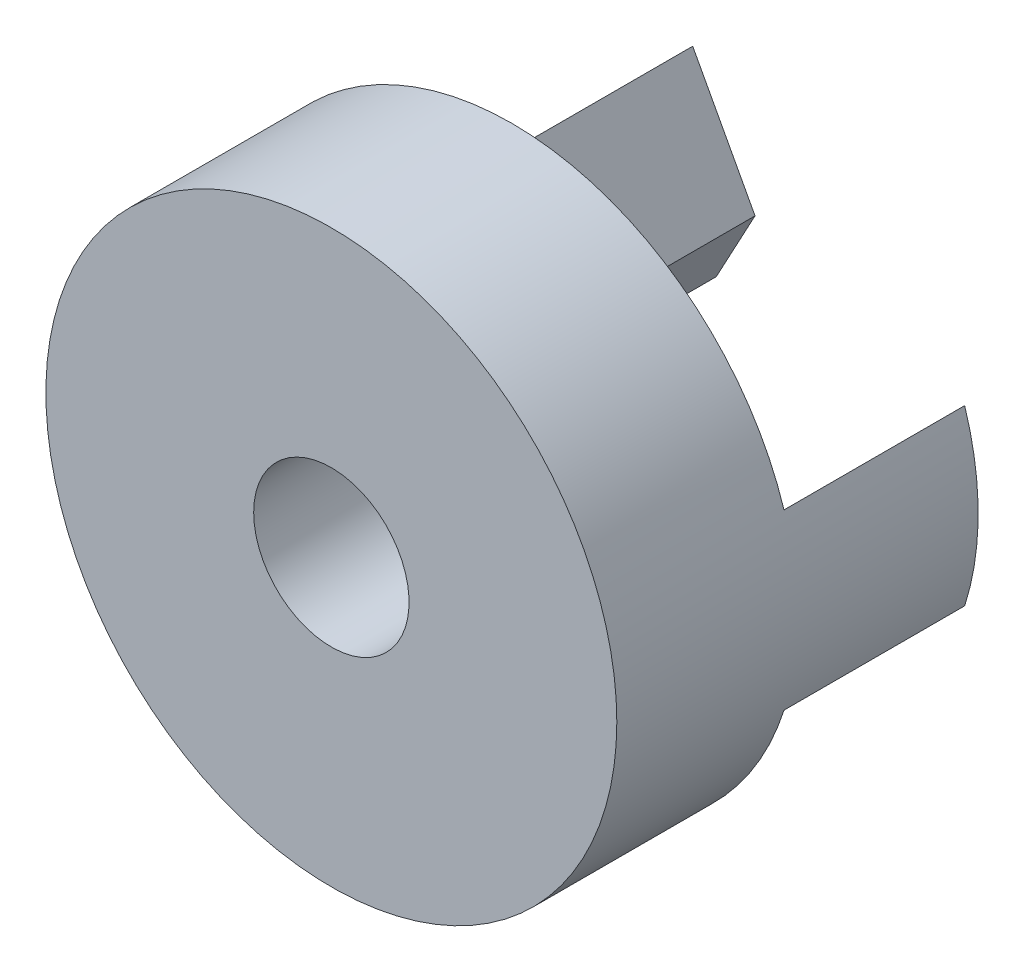
SolidWorks part; units mm, degrees
ref_plane "Front Plane" through (0, 0, 0) normal (0, 0, 1) x (1, 0, 0)
ref_plane "Top Plane" through (0, 0, 0) normal (0, 1, 0) x (1, 0, 0)
ref_plane "Right Plane" through (0, 0, 0) normal (1, 0, 0) x (0, 0, -1)
sketch "Sketch1" plane through (0, 0, 0) normal (0, 0, 1) x (1, 0, 0)
  circle A0 centre (0, 0) radius 20.066
  dimension "D1" = 40.132
extrude "Boss-Extrude1" add sketch "Sketch1" along normal blind 12.7
sketch "Sketch2" plane through (0, 0, 0) normal (0, 0, -1) x (-1, 0, 0)
  circle A0 centre (0, 0) radius 5.461
  dimension "D1" = 10.922
extrude "Cut-Extrude1" cut sketch "Sketch2" against normal through all
sketch "Sketch3" plane through (0, 0, 0) normal (0, 0, -1) x (-1, 0, 0)
  line L0 (-19.1176, -6.096) -> (-14.9225, 0)
  line L1 (-14.9225, 0) -> (-19.1176, 6.096)
  line L2 (19.1176, 6.096) -> (14.9225, 0)
  line L3 (14.9225, 0) -> (19.1176, -6.096)
  line L4 (0, 18.415) -> (-4.3815, 10.277)
  line L5 (-4.3815, 10.277) -> (-1.651, 5.2055)
  line L6 (1.651, 5.2055) -> (4.3815, 10.277)
  line L7 (4.3815, 10.277) -> (0, 18.415)
  line L8 (-1.651, -5.2055) -> (-4.3815, -10.277)
  line L9 (-4.3815, -10.277) -> (0, -18.415)
  line L10 (0, -18.415) -> (4.3815, -10.277)
  line L11 (4.3815, -10.277) -> (1.651, -5.2055)
  line L12 (-1.651, 5.2055) -> (0, 2.1389) construction
  line L13 (0, 2.1389) -> (1.651, 5.2055) construction
  line L14 (0, 10.277) -> (0, 2.1389) construction
  line L15 (0, 10.277) -> (0, 18.415) construction
  circle A0 centre (0, 0) radius 20.066 construction
  circle A1 centre (0, 0) radius 5.461 construction
  arc A2 (-19.1176, 6.096) -> (-19.1176, -6.096) centre (0, 0) ccw
  arc A3 (19.1176, 6.096) -> (19.1176, -6.096) centre (0, 0) cw
  arc A4 (-1.651, 5.2055) -> (1.651, 5.2055) centre (0, 0) cw
  arc A5 (-1.651, -5.2055) -> (1.651, -5.2055) centre (0, 0) ccw
  point P23 (0, -5.461)
  dimension "D1" = 14.9225
  dimension "D2" = 12.192
  dimension "D3" = 18.415
  dimension "D4" = 8.763
  dimension "D5" = 3.302
extrude "Boss-Extrude2" add sketch "Sketch3" along normal blind 12.7
